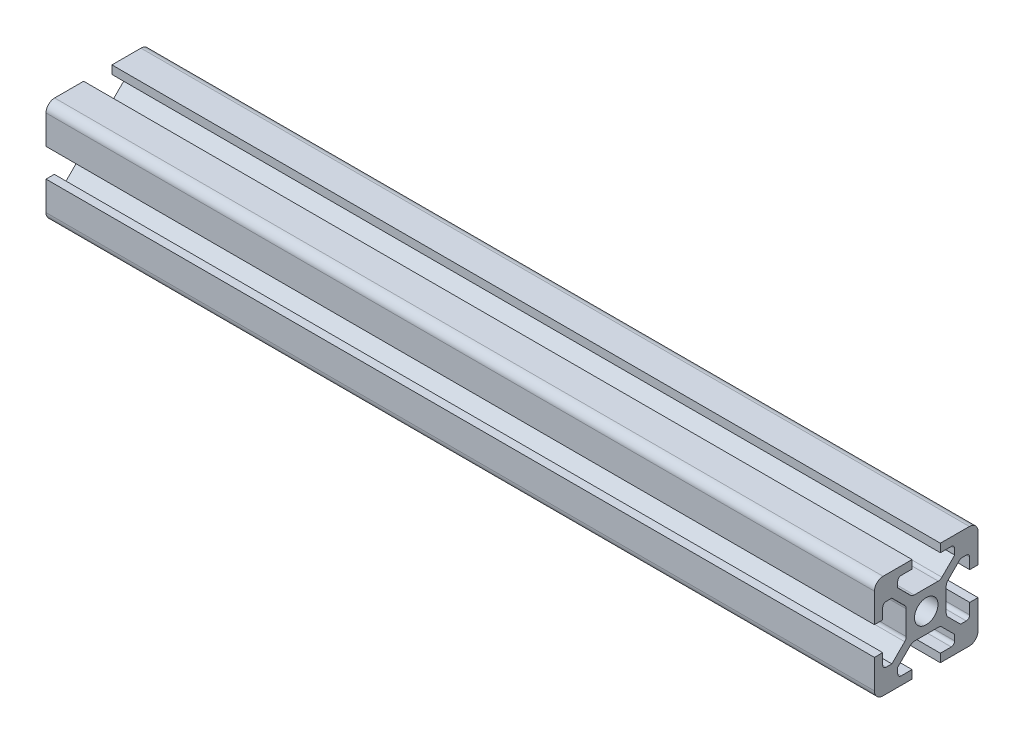
SolidWorks part; units mm, degrees
ref_plane "Front Plane" through (0, 0, 0) normal (0, 0, 1) x (1, 0, 0)
ref_plane "Top Plane" through (0, 0, 0) normal (0, 1, 0) x (1, 0, 0)
ref_plane "Right Plane" through (0, 0, 0) normal (1, 0, 0) x (0, 0, -1)
sketch "Sketch1" plane through (0, 0, 0) normal (1, 0, 0) x (0, 0, -1)
  line L0 (10.9, 0) -> (10.9, 2.4)
  line L1 (0, 0) -> (10.9, 0)
  line L2 (0, 0) -> (0, 10.9)
  line L3 (0, 30) -> (10.9, 30)
  line L4 (30, 0) -> (30, 10.9)
  line L5 (19.1, 0) -> (19.1, 2.4)
  line L6 (0, 10.9) -> (2.4, 10.9)
  line L7 (0, 19.1) -> (2.4, 19.1)
  line L8 (10.9, 30) -> (10.9, 27.6)
  line L9 (19.1, 30) -> (19.1, 27.6)
  line L10 (30, 19.1) -> (27.6, 19.1)
  line L11 (27.6, 10.9) -> (30, 10.9)
  line L12 (24.95, 23.25) -> (27.6, 23.25)
  line L18 (6.75, 2.4) -> (10.9, 2.4)
  line L19 (27.6, 6.75) -> (27.6, 10.9)
  line L20 (2.4, 6.75) -> (2.4, 10.9)
  line L21 (6.75, 27.6) -> (10.9, 27.6)
  line L22 (19.1, 2.4) -> (23.25, 2.4)
  line L23 (27.6, 19.1) -> (27.6, 23.25)
  line L24 (2.4, 19.1) -> (2.4, 23.25)
  line L25 (19.1, 27.6) -> (23.25, 27.6)
  line L26 (19.1, 20.8) -> (10.9, 20.8)
  line L29 (5.05, 6.75) -> (2.4, 6.75)
  line L31 (2.4, 23.25) -> (5.05, 23.25)
  line L34 (6.75, 24.95) -> (6.75, 27.6)
  line L40 (23.25, 2.4) -> (23.25, 5.05)
  line L43 (9.2, 10.9) -> (9.2, 19.1)
  line L44 (19.1, 9.2) -> (10.9, 9.2)
  line L45 (20.8, 10.9) -> (20.8, 19.1)
  line L46 (24.95, 6.75) -> (20.8, 10.9)
  line L47 (19.1, 9.2) -> (23.25, 5.05)
  line L48 (20.8, 19.1) -> (24.95, 23.25)
  line L49 (10.9, 9.2) -> (6.75, 5.05)
  line L50 (5.05, 6.75) -> (9.2, 10.9)
  line L51 (19.1, 20.8) -> (23.25, 24.95)
  line L52 (6.75, 24.95) -> (10.9, 20.8)
  line L53 (5.05, 23.25) -> (9.2, 19.1)
  line L54 (19.1, 30) -> (30, 30)
  line L55 (30, 19.1) -> (30, 30)
  line L56 (19.1, 0) -> (30, 0)
  line L57 (0, 19.1) -> (0, 30)
  line L58 (6.75, 5.05) -> (6.75, 2.4)
  line L59 (24.95, 6.75) -> (27.6, 6.75)
  line L60 (23.25, 27.6) -> (23.25, 24.95)
  circle A0 centre (15, 15) radius 3.4
  point P5 (10.9, 0)
  point P6 (19.1, 0)
  point P7 (0, 10.9)
  point P8 (0, 19.1)
  point P9 (30, 19.1)
  point P10 (30, 10.9)
  point P11 (19.1, 30)
  point P12 (10.9, 30)
  point P59 (15, 20.8)
  point P61 (9.2, 15)
  point P62 (15, 9.2)
  point P65 (20.8, 15)
  point P67 (24.95, 6.75)
  point P70 (15, 20.8)
  point P73 (9.2, 15)
  point P76 (15, 9.2)
  point P79 (20.8, 15)
  point P80 (23.25, 5.05)
  point P81 (24.95, 23.25)
  point P82 (6.75, 5.05)
  point P84 (5.05, 6.75)
  point P88 (23.25, 24.95)
  point P90 (6.75, 24.95)
  point P92 (5.05, 23.25)
extrude "Boss-Extrude2" add sketch "Sketch1" along normal blind 100
fillet "Fillet5" radius 2.5 4 edges at (50, 0, -30) (50, 30, -30) (50, 0, 0) (50, 30, 0)
fillet "Fillet6" radius 1.5 6 edges at (50, 19.1, -20.8) (50, 10.9, -20.8) (50, 9.2, -10.9) (50, 9.2, -19.1) (50, 10.9, -9.2) (50, 19.1, -9.2)
fillet "Fillet7" radius 1.5 2 edges at (50, 20.8, -19.1) (50, 20.8, -10.9)
fillet "Fillet8" radius 1 8 edges at (50, 23.25, -2.4) (50, 27.6, -6.75) (50, 27.6, -23.25) (50, 23.25, -27.6) (50, 6.75, -27.6) (50, 2.4, -23.25) (50, 2.4, -6.75) (50, 6.75, -2.4)
sketch "Sketch3" plane through (0, 0, 0) normal (1, 0, 0) x (0, 0, -1)
  line L0 (10.9, 27.6) -> (10.9, 30) construction
  line L1 (7.75, 27.6) -> (10.9, 27.6) construction
  line L2 (6.75, 24.95) -> (6.75, 26.6) construction
  line L3 (10.4607, 21.2393) -> (6.75, 24.95) construction
  line L4 (18.4787, 20.8) -> (11.5213, 20.8) construction
  line L5 (23.25, 24.95) -> (19.5393, 21.2393) construction
  line L6 (23.25, 26.6) -> (23.25, 24.95) construction
  line L7 (19.1, 27.6) -> (22.25, 27.6) construction
  line L8 (19.1, 30) -> (19.1, 27.6) construction
  line L9 (27.5, 30) -> (19.1, 30) construction
  line L10 (30, 19.1) -> (30, 27.5) construction
  line L11 (27.6, 19.1) -> (30, 19.1) construction
  line L12 (27.6, 22.25) -> (27.6, 19.1) construction
  line L13 (24.95, 23.25) -> (26.6, 23.25) construction
  line L14 (21.2393, 19.5393) -> (24.95, 23.25) construction
  line L15 (20.8, 11.5213) -> (20.8, 18.4787) construction
  line L16 (24.95, 6.75) -> (21.2393, 10.4607) construction
  line L17 (26.6, 6.75) -> (24.95, 6.75) construction
  line L18 (27.6, 10.9) -> (27.6, 7.75) construction
  line L19 (30, 10.9) -> (27.6, 10.9) construction
  line L20 (30, 2.5) -> (30, 10.9) construction
  line L21 (19.1, 0) -> (27.5, 0) construction
  line L22 (19.1, 2.4) -> (19.1, 0) construction
  line L23 (22.25, 2.4) -> (19.1, 2.4) construction
  line L24 (23.25, 5.05) -> (23.25, 3.4) construction
  line L25 (19.5393, 8.7607) -> (23.25, 5.05) construction
  line L26 (11.5213, 9.2) -> (18.4787, 9.2) construction
  line L27 (6.75, 5.05) -> (10.4607, 8.7607) construction
  line L28 (6.75, 3.4) -> (6.75, 5.05) construction
  line L29 (10.9, 2.4) -> (7.75, 2.4) construction
  line L30 (10.9, 0) -> (10.9, 2.4) construction
  line L31 (2.5, 0) -> (10.9, 0) construction
  line L32 (0, 10.9) -> (0, 2.5) construction
  line L33 (2.4, 10.9) -> (0, 10.9) construction
  line L34 (2.4, 7.75) -> (2.4, 10.9) construction
  line L35 (5.05, 6.75) -> (3.4, 6.75) construction
  line L36 (8.7607, 10.4607) -> (5.05, 6.75) construction
  line L37 (9.2, 18.4787) -> (9.2, 11.5213) construction
  line L38 (5.05, 23.25) -> (8.7607, 19.5393) construction
  line L39 (3.4, 23.25) -> (5.05, 23.25) construction
  line L40 (2.4, 19.1) -> (2.4, 22.25) construction
  line L41 (0, 19.1) -> (2.4, 19.1) construction
  line L42 (0, 27.5) -> (0, 19.1) construction
  line L43 (10.9, 30) -> (2.5, 30) construction
  line L44 (10.9, 27.6) -> (10.9, 30)
  line L45 (7.75, 27.6) -> (10.9, 27.6)
  line L46 (6.75, 24.95) -> (6.75, 26.6)
  line L47 (10.4607, 21.2393) -> (6.75, 24.95)
  line L48 (18.4787, 20.8) -> (11.5213, 20.8)
  line L49 (23.25, 24.95) -> (19.5393, 21.2393)
  line L50 (23.25, 26.6) -> (23.25, 24.95)
  line L51 (19.1, 27.6) -> (22.25, 27.6)
  line L52 (19.1, 30) -> (19.1, 27.6)
  line L53 (27.5, 30) -> (19.1, 30)
  line L54 (30, 19.1) -> (30, 27.5)
  line L55 (27.6, 19.1) -> (30, 19.1)
  line L56 (27.6, 22.25) -> (27.6, 19.1)
  line L57 (24.95, 23.25) -> (26.6, 23.25)
  line L58 (21.2393, 19.5393) -> (24.95, 23.25)
  line L59 (20.8, 11.5213) -> (20.8, 18.4787)
  line L60 (24.95, 6.75) -> (21.2393, 10.4607)
  line L61 (26.6, 6.75) -> (24.95, 6.75)
  line L62 (27.6, 10.9) -> (27.6, 7.75)
  line L63 (30, 10.9) -> (27.6, 10.9)
  line L64 (30, 2.5) -> (30, 10.9)
  line L65 (19.1, 0) -> (27.5, 0)
  line L66 (19.1, 2.4) -> (19.1, 0)
  line L67 (22.25, 2.4) -> (19.1, 2.4)
  line L68 (23.25, 5.05) -> (23.25, 3.4)
  line L69 (19.5393, 8.7607) -> (23.25, 5.05)
  line L70 (11.5213, 9.2) -> (18.4787, 9.2)
  line L71 (6.75, 5.05) -> (10.4607, 8.7607)
  line L72 (6.75, 3.4) -> (6.75, 5.05)
  line L73 (10.9, 2.4) -> (7.75, 2.4)
  line L74 (10.9, 0) -> (10.9, 2.4)
  line L75 (2.5, 0) -> (10.9, 0)
  line L76 (0, 10.9) -> (0, 2.5)
  line L77 (2.4, 10.9) -> (0, 10.9)
  line L78 (2.4, 7.75) -> (2.4, 10.9)
  line L79 (5.05, 6.75) -> (3.4, 6.75)
  line L80 (8.7607, 10.4607) -> (5.05, 6.75)
  line L81 (9.2, 18.4787) -> (9.2, 11.5213)
  line L82 (5.05, 23.25) -> (8.7607, 19.5393)
  line L83 (3.4, 23.25) -> (5.05, 23.25)
  line L84 (2.4, 19.1) -> (2.4, 22.25)
  line L85 (0, 19.1) -> (2.4, 19.1)
  line L86 (0, 27.5) -> (0, 19.1)
  line L87 (10.9, 30) -> (2.5, 30)
  circle A0 centre (15, 15) radius 3.4 construction
  arc A1 (7.75, 27.6) -> (6.75, 26.6) centre (7.75, 26.6) ccw construction
  arc A2 (10.4607, 21.2393) -> (11.5213, 20.8) centre (11.5213, 22.3) ccw construction
  arc A3 (18.4787, 20.8) -> (19.5393, 21.2393) centre (18.4787, 22.3) ccw construction
  arc A4 (23.25, 26.6) -> (22.25, 27.6) centre (22.25, 26.6) ccw construction
  arc A5 (30, 27.5) -> (27.5, 30) centre (27.5, 27.5) ccw construction
  arc A6 (27.6, 22.25) -> (26.6, 23.25) centre (26.6, 22.25) ccw construction
  arc A7 (21.2393, 19.5393) -> (20.8, 18.4787) centre (22.3, 18.4787) ccw construction
  arc A8 (20.8, 11.5213) -> (21.2393, 10.4607) centre (22.3, 11.5213) ccw construction
  arc A9 (26.6, 6.75) -> (27.6, 7.75) centre (26.6, 7.75) ccw construction
  arc A10 (27.5, 0) -> (30, 2.5) centre (27.5, 2.5) ccw construction
  arc A11 (22.25, 2.4) -> (23.25, 3.4) centre (22.25, 3.4) ccw construction
  arc A12 (19.5393, 8.7607) -> (18.4787, 9.2) centre (18.4787, 7.7) ccw construction
  arc A13 (11.5213, 9.2) -> (10.4607, 8.7607) centre (11.5213, 7.7) ccw construction
  arc A14 (6.75, 3.4) -> (7.75, 2.4) centre (7.75, 3.4) ccw construction
  arc A15 (0, 2.5) -> (2.5, 0) centre (2.5, 2.5) ccw construction
  arc A16 (2.4, 7.75) -> (3.4, 6.75) centre (3.4, 7.75) ccw construction
  arc A17 (9.2, 18.4787) -> (8.7607, 19.5393) centre (7.7, 18.4787) ccw construction
  arc A18 (8.7607, 10.4607) -> (9.2, 11.5213) centre (7.7, 11.5213) ccw construction
  arc A19 (3.4, 23.25) -> (2.4, 22.25) centre (3.4, 22.25) ccw construction
  arc A20 (2.5, 30) -> (0, 27.5) centre (2.5, 27.5) ccw construction
  circle A21 centre (15, 15) radius 3.4
  arc A22 (7.75, 27.6) -> (6.75, 26.6) centre (7.75, 26.6) ccw
  arc A23 (10.4607, 21.2393) -> (11.5213, 20.8) centre (11.5213, 22.3) ccw
  arc A24 (18.4787, 20.8) -> (19.5393, 21.2393) centre (18.4787, 22.3) ccw
  arc A25 (23.25, 26.6) -> (22.25, 27.6) centre (22.25, 26.6) ccw
  arc A26 (30, 27.5) -> (27.5, 30) centre (27.5, 27.5) ccw
  arc A27 (27.6, 22.25) -> (26.6, 23.25) centre (26.6, 22.25) ccw
  arc A28 (21.2393, 19.5393) -> (20.8, 18.4787) centre (22.3, 18.4787) ccw
  arc A29 (20.8, 11.5213) -> (21.2393, 10.4607) centre (22.3, 11.5213) ccw
  arc A30 (26.6, 6.75) -> (27.6, 7.75) centre (26.6, 7.75) ccw
  arc A31 (27.5, 0) -> (30, 2.5) centre (27.5, 2.5) ccw
  arc A32 (22.25, 2.4) -> (23.25, 3.4) centre (22.25, 3.4) ccw
  arc A33 (19.5393, 8.7607) -> (18.4787, 9.2) centre (18.4787, 7.7) ccw
  arc A34 (11.5213, 9.2) -> (10.4607, 8.7607) centre (11.5213, 7.7) ccw
  arc A35 (6.75, 3.4) -> (7.75, 2.4) centre (7.75, 3.4) ccw
  arc A36 (0, 2.5) -> (2.5, 0) centre (2.5, 2.5) ccw
  arc A37 (2.4, 7.75) -> (3.4, 6.75) centre (3.4, 7.75) ccw
  arc A38 (9.2, 18.4787) -> (8.7607, 19.5393) centre (7.7, 18.4787) ccw
  arc A39 (8.7607, 10.4607) -> (9.2, 11.5213) centre (7.7, 11.5213) ccw
  arc A40 (3.4, 23.25) -> (2.4, 22.25) centre (3.4, 22.25) ccw
  arc A41 (2.5, 30) -> (0, 27.5) centre (2.5, 27.5) ccw
extrude "Boss-Extrude3" add sketch "Sketch3" against normal blind 140
